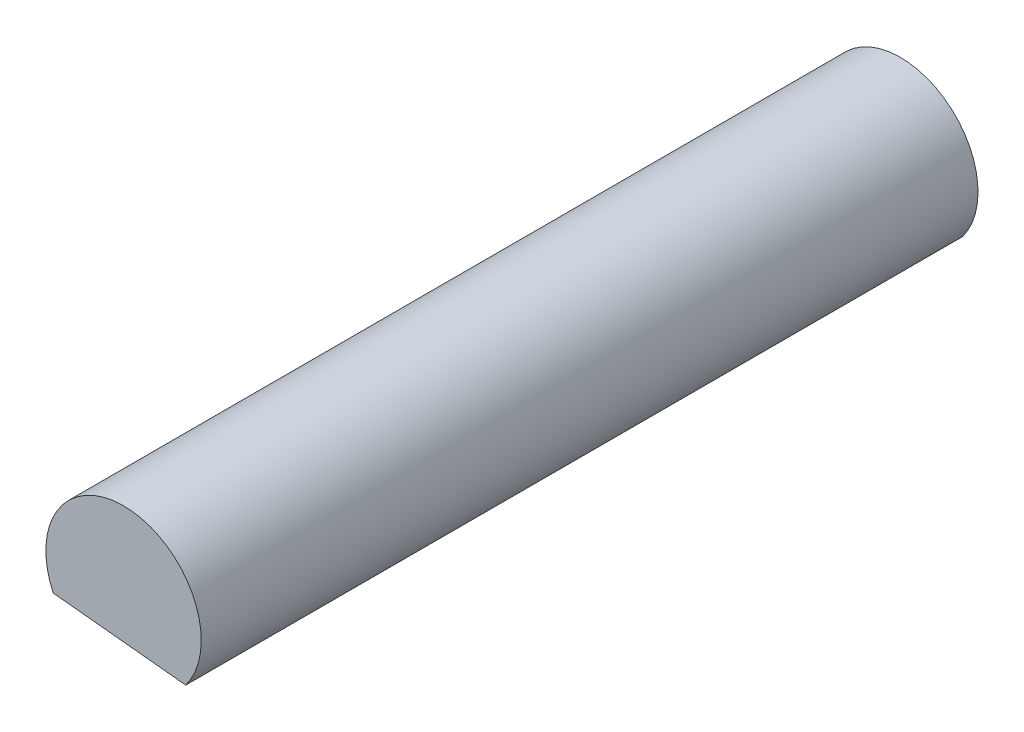
SolidWorks part; units mm, degrees
ref_plane "Front Plane" through (0, 0, 0) normal (0, 0, 1) x (1, 0, 0)
ref_plane "Top Plane" through (0, 0, 0) normal (0, 1, 0) x (1, 0, 0)
ref_plane "Right Plane" through (0, 0, 0) normal (1, 0, 0) x (0, 0, -1)
sketch "Sketch1" plane through (0, 0, 0) normal (0, 0, 1) x (1, 0, 0)
  line L0 (28.0198, -20.9735) -> (-31.6716, -14.8966)
  arc A0 (28.0198, -20.9735) -> (-31.6716, -14.8966) centre (0, 0) ccw
  dimension "D1" = 70
  dimension "D2" = 60
extrude "Boss-Extrude1" add sketch "Sketch1" along normal blind 350
